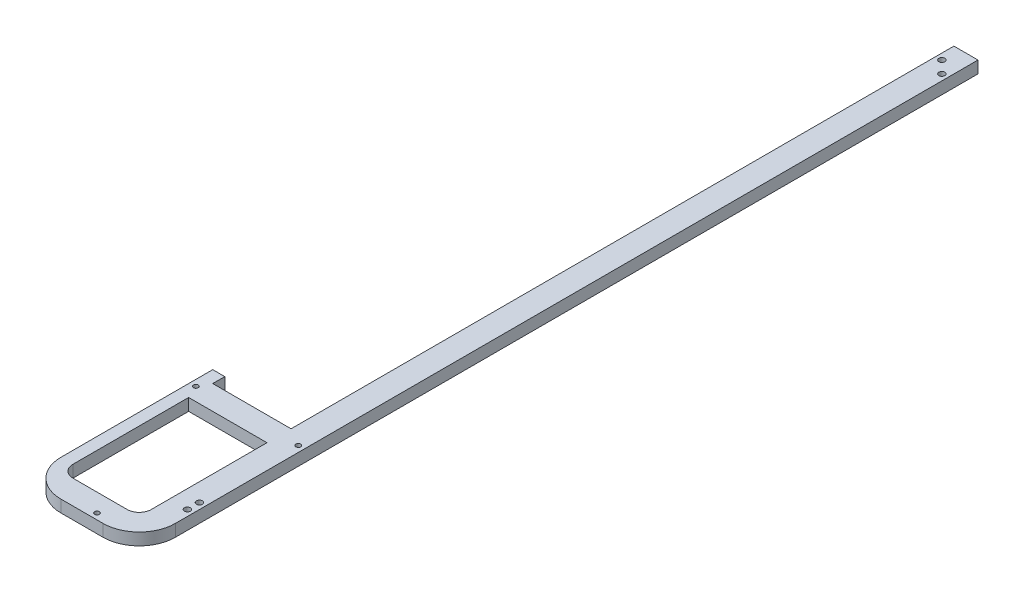
SolidWorks part; units mm, degrees
ref_plane "Front Plane" through (0, 0, 0) normal (0, 0, 1) x (1, 0, 0)
ref_plane "Top Plane" through (0, 0, 0) normal (0, 1, 0) x (1, 0, 0)
ref_plane "Right Plane" through (0, 0, 0) normal (1, 0, 0) x (0, 0, -1)
sketch "Sketch1" plane through (0, 0, 0) normal (0, 1, 0) x (1, 0, 0)
  line L1 (-47.5, -70) -> (47.5, -70)
  line L2 (-47.5, -70) -> (-47.5, 86)
  line L3 (-47.5, 86) -> (-37.5, 86)
  line L5 (-37.5, -60) -> (-37.5, 52)
  line L7 (-37.5, -60) -> (37.5, -60)
  line L11 (-37.5, 76) -> (-37.5, 86)
  line L12 (-37.5, 76) -> (27.5, 76)
  line L17 (-37.5, 52) -> (37.5, 52)
  line L19 (37.5, 52) -> (37.5, -60)
  line L20 (47.5, 32) -> (47.5, -70)
  line L22 (27.5, 76) -> (27.5, 626)
  line L23 (27.5, 626) -> (47.5, 626)
  line L24 (47.5, 32) -> (47.5, 626)
  line L27 (37.5, -30) -> (37.5, -10)
  line L29 (-37.5, -30) -> (-37.5, -10)
  point P0 (0, 0)
  point P6 (0, 0)
  dimension "D1" = 156
  dimension "D2" = 10
  dimension "D3" = 75
  dimension "D4" = 10
  dimension "D5" = 95
  dimension "D6" = 60
  dimension "D7" = 37.5
  dimension "D8" = 10
  dimension "D9" = 24
  dimension "D10" = 550
  dimension "D11" = 20
extrude "Boss-Extrude1" add sketch "Sketch1" along normal blind 10
fillet "Fillet2" radius 30 2 edges at (-47.5, 5, 70) (47.5, 5, 70)
sketch "Sketch2" plane through (0, 10, 0) normal (0, 1, 0) x (1, 0, 0)
  line L1 (-47.5, 86) -> (-37.5, 86) construction
  line L4 (-37.5, 76) -> (-37.5, 86) construction
  line L5 (47.5, 626) -> (47.5, -40) construction
  circle A0 centre (-42.5, 67) radius 2
  circle A1 centre (42.5, 67) radius 2
  circle A2 centre (7.5, -65) radius 2
  dimension "D2" = 4
  dimension "D3" = 4
  dimension "D6" = 5
  dimension "D7" = 4
  dimension "D1" = 19
  dimension "D4" = 5
  dimension "D5" = 0
  dimension "D8" = 132
  dimension "D9" = 50
extrude "Cut-Extrude1" cut sketch "Sketch2" against normal blind 10
sketch "Sketch3" plane through (0, 10, 0) normal (0, 1, 0) x (1, 0, 0)
  line L3 (27.5, 626) -> (47.5, 626) construction
  circle A0 centre (42.5, 601) radius 2.5
  circle A1 centre (32.5, 611) radius 2.5
  dimension "D5" = 5
  dimension "D6" = 5
  dimension "D1" = 25
  dimension "D2" = 15
extrude "Cut-Extrude2" cut sketch "Sketch3" against normal blind 10
sketch "Sketch4" plane through (0, 10, 0) normal (0, 1, 0) x (1, 0, 0)
  circle A0 centre (42.5, -25) radius 2.5
  circle A1 centre (42.5, -15) radius 2.5
  dimension "D3" = 5
  dimension "D4" = 5
extrude "Cut-Extrude3" cut sketch "Sketch4" against normal through all
sketch "Sketch5" plane through (0, 10, 0) normal (0, 1, 0) x (1, 0, 0)
  line L0 (27.5, 76) -> (27.5, 626) construction
  line L1 (-37.5, 56) -> (27.5, 56)
  line L2 (-37.5, 56) -> (-37.5, -50)
  line L3 (-37.5, -50) -> (27.5, -50)
  line L4 (27.5, 56) -> (27.5, -50)
  line L5 (-37.5, 76) -> (-37.5, 86) construction
  line L6 (-37.5, 76) -> (27.5, 76) construction
  line L7 (-17.5, -70) -> (17.5, -70) construction
  dimension "D1" = 0
  dimension "D2" = 0
  dimension "D3" = 20
  dimension "D4" = 20
extrude "Cut-Extrude4" cut sketch "Sketch5" against normal through all contours L3 L4 L1 L2
fillet "Fillet3" radius 10 2 edges at (27.5, 5, 50) (-37.5, 5, 50)
